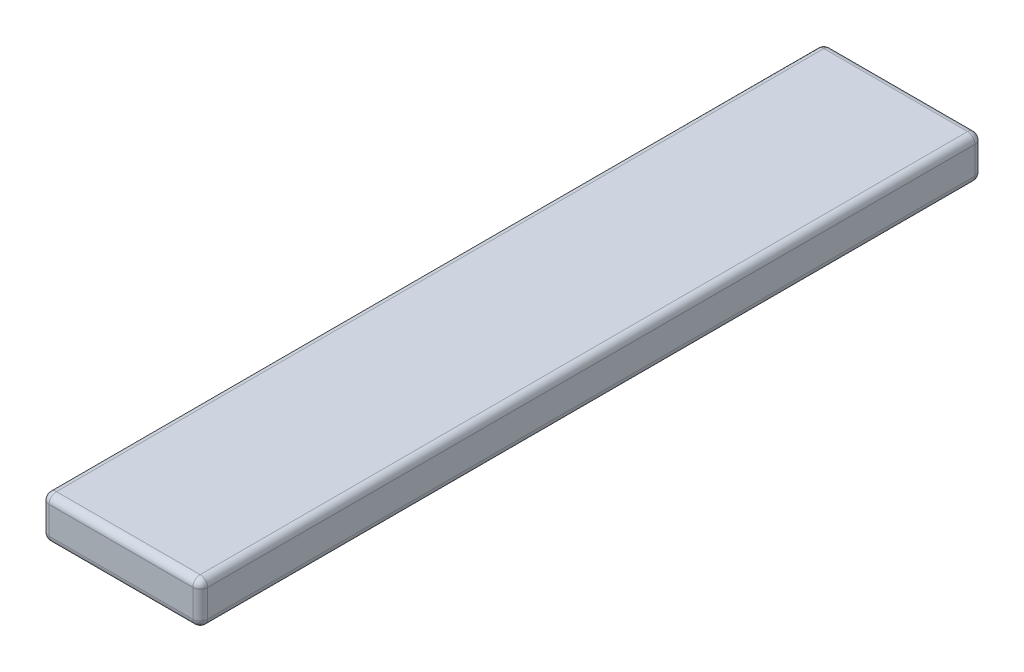
SolidWorks part; units mm, degrees
ref_plane "Front Plane" through (0, 0, 0) normal (0, 0, 1) x (1, 0, 0)
ref_plane "Top Plane" through (0, 0, 0) normal (0, 1, 0) x (1, 0, 0)
ref_plane "Right Plane" through (0, 0, 0) normal (1, 0, 0) x (0, 0, -1)
sketch "Sketch1" plane through (0, 0, 0) normal (0, 1, 0) x (1, 0, 0)
  line L1 (-375, 964.6947) -> (375, 964.6947)
  line L2 (-375, 964.6947) -> (-375, -2735.3053)
  line L3 (-375, -2735.3053) -> (375, -2735.3053)
  line L4 (375, 964.6947) -> (375, -2735.3053)
  line L5 (-375, 964.6947) -> (375, -2735.3053) construction
  line L6 (-375, -2735.3053) -> (375, 964.6947) construction
  point P0 (0, 0)
  point P5 (-375, -2735.3053)
  dimension "D1" = 750
  dimension "D2" = 3700
extrude "Boss-Extrude1" add sketch "Sketch1" along normal blind 200
fillet "Fillet1" radius 35 12 edges at (375, 100, -964.6947) (-375, 100, -964.6947) (-375, 100, 2735.3053) (375, 100, 2735.3053) (0, 200, 2735.3053) (-375, 200, 885.3053) (0, 200, -964.6947) (375, 200, 885.3053) (0, 0, -964.6947) (-375, 0, 885.3053) (0, 0, 2735.3053) (375, 0, 885.3053)
